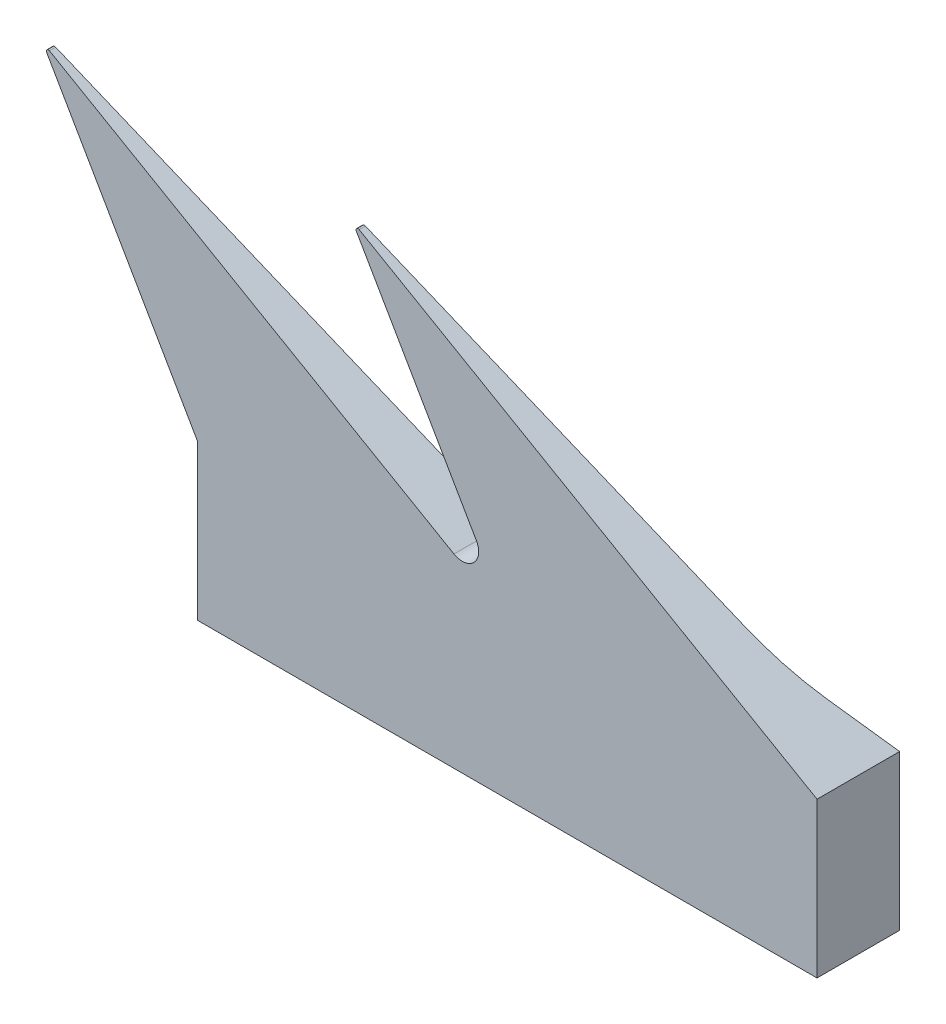
SolidWorks part; units mm, degrees
ref_plane "Front Plane" through (0, 0, 0) normal (0, 0, 1) x (1, 0, 0)
ref_plane "Top Plane" through (0, 0, 0) normal (0, 1, 0) x (1, 0, 0)
ref_plane "Right Plane" through (0, 0, 0) normal (1, 0, 0) x (0, 0, -1)
sketch "Sketch1" plane through (0, 0, 0) normal (0, 0, 1) x (1, 0, 0)
  line L0 (-1.5, 0.0241) -> (1.5, 0.0241)
  line L3 (-1.5, 0.0241) -> (1.5, 0.0241)
  line L4 (-2.2177, 1.3045) -> (-0.2586, 0.1734)
  line L5 (-1.5, 0.0241) -> (-1.5, -0.7259)
  line L6 (-1.5, 0.0241) -> (-2.2313, 1.2908)
  line L7 (-1.5, -0.7259) -> (1.5, -0.7259)
  line L8 (1.5, 0.0241) -> (-0.7177, 1.3045)
  line L9 (1.5, 0.0241) -> (1.5, -0.7259)
  line L10 (-0.1493, 0.2827) -> (-0.7313, 1.2908)
  arc A0 (-0.1493, 0.2827) -> (-0.2586, 0.1734) centre (-0.2186, 0.2427) cw
  arc A1 (-2.2177, 1.3045) -> (-2.2313, 1.2908) centre (-2.2227, 1.2958) ccw
  arc A2 (-0.7177, 1.3045) -> (-0.7313, 1.2908) centre (-0.7227, 1.2958) ccw
  point P9 (0.0616, 1.75)
  point P12 (-2.25, 1.3231)
  point P15 (-0.75, 1.3231)
  point P17 (0.0616, 1.75)
  dimension "D2" = 0.08
  dimension "D4" = 0.01
  dimension "D5" = 0.01
  dimension "D1" = 3
  dimension "D3" = 0.75
  dimension "D6" = 1.5
extrude "Boss-Extrude2" add sketch "Sketch1" along normal blind 0.4 contours L9 L0 L5 L7 | L8 A2 L10 A0 L4 A1 L6 L0
ref_plane "Plane1" through (1.5, 0, 0) normal (1, 0, 0) x (0, 0, -1)
sketch "Sketch3" plane through (1.5, 0, 0) normal (1, 0, 0) x (0, 0, -1)
  line L0 (-0.3955, 1.4321) -> (-0.1803, 0.3562)
  line L1 (-0.1007, 0.169) -> (0, 0.0241)
  line L2 (-0.3955, 1.4321) -> (0, 1.4321)
  line L3 (0, 1.4321) -> (0, 0.0241)
  arc A0 (-0.1007, 0.169) -> (-0.1803, 0.3562) centre (0.31, 0.4542) cw
  dimension "D1" = 0.5
extrude "Cut-Extrude2" cut sketch "Sketch3" against normal blind 7.4
ref_plane "Plane2" through (0, 0, 0.4) normal (0, 0, 1) x (1, 0, 0)
